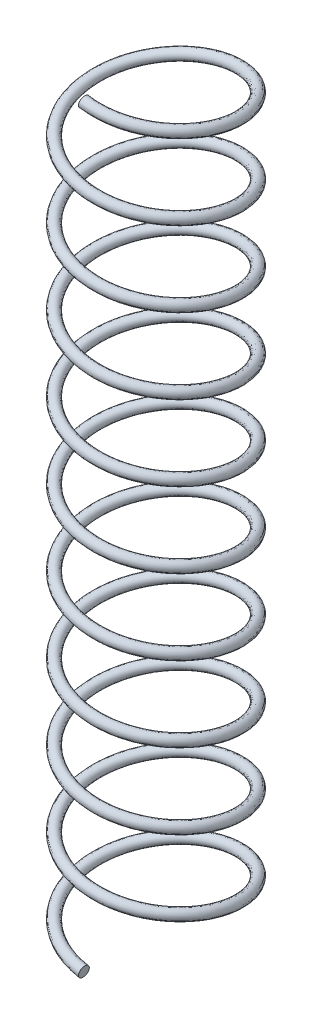
SolidWorks part; units mm, degrees
ref_plane "Front Plane" through (0, 0, 0) normal (0, 0, 1) x (1, 0, 0)
ref_plane "Top Plane" through (0, 0, 0) normal (0, 1, 0) x (1, 0, 0)
ref_plane "Right Plane" through (0, 0, 0) normal (1, 0, 0) x (0, 0, -1)
sketch "Sketch1" plane through (0, 0, 0) normal (0, 1, 0) x (1, 0, 0)
  circle A0 centre (0, 0) radius 6.7
  dimension "D1" = 13.4
curve "Helix/Spiral1" pitch 7 height 70 turns 10
sweep "Sweep1" add path "Helix/Spiral1" circular profile diameter 1 parameters "D3"=1
